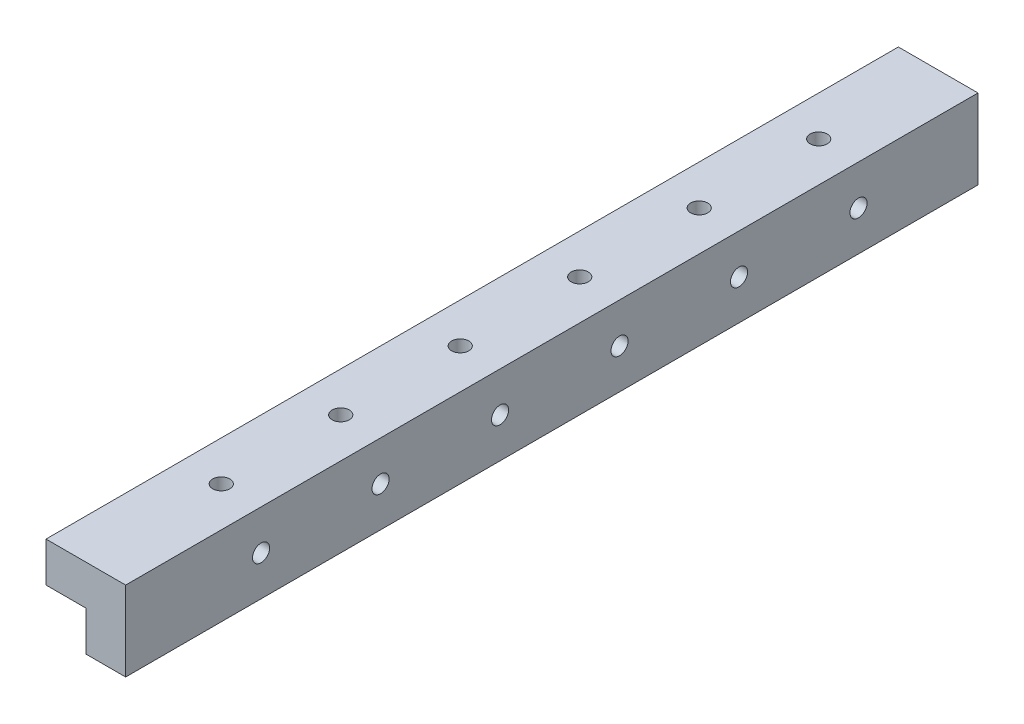
SolidWorks part; units mm, degrees
ref_plane "Front Plane" through (0, 0, 0) normal (0, 0, 1) x (1, 0, 0)
ref_plane "Top Plane" through (0, 0, 0) normal (0, 1, 0) x (1, 0, 0)
ref_plane "Right Plane" through (0, 0, 0) normal (1, 0, 0) x (0, 0, -1)
sketch "Sketch1" plane through (0, 0, 0) normal (0, 0, 1) x (1, 0, 0)
  line L0 (0, -10) -> (10, -10)
  line L1 (10, -10) -> (10, 10)
  line L2 (10, 10) -> (-10, 10)
  line L3 (-10, 10) -> (-10, 0)
  line L4 (-10, 0) -> (0, 0)
  line L5 (0, 0) -> (0, -10)
  point P3 (0, 0)
  dimension "D1" = 10
  dimension "D2" = 20
  dimension "D3" = 10
  dimension "D4" = 20
extrude "Boss-Extrude1" add sketch "Sketch1" against normal blind 214
hole_wizard "Tap Drill for M3x0.5 Tap1" positions "Sketch70" profile "Sketch72" hole size "M3x0.5" standard "ANSI Metric"
sketch "Sketch70" plane through (10, 0, 0) normal (1, 0, 0) x (0, 0, -1)
  line L0 (214, -10) -> (214, 10) construction
  point P0 (34, 0)
  point P3 (64, 0)
  point P6 (94, 0)
  point P9 (124, 0)
  point P12 (154, 0)
  point P15 (184, 0)
  dimension "D1" = 34
  dimension "D2" = 30
  dimension "D3" = 60
  dimension "D4" = 90
  dimension "D5" = 120
  dimension "D6" = 150
  dimension "D7" = 30
sketch "Sketch72" plane through (10, 0, -34) normal (0, 1, 0) x (0, 0, -1)
  line L0 (0, 0) -> (0, 6.825)
  line L1 (0, 6.825) -> (2.15, 6.825)
  line L2 (2.15, 6.825) -> (2.15, 0)
  line L5 (2.15, 0) -> (0, 0)
  line L10 (0, 6.825) -> (-2.15, 6.825) construction
  line L11 (0, -6.35) -> (0, 107.95) construction
  dimension "Hole Dia." = 4.3
  dimension "Hole Depth" = 6.825
  dimension "Drill Angle" = 180
hole_wizard "Tap Drill for M3x0.5 Tap2" positions "Sketch75" profile "Sketch76" hole size "M3x0.5" standard "ANSI Metric"
sketch "Sketch75" plane through (0, 10, 0) normal (0, 1, 0) x (1, 0, 0)
  line L0 (10, 0) -> (-10, 0) construction
  line L1 (10, 214) -> (-10, 214) construction
  point P0 (0, 34)
  point P3 (0, 64)
  point P6 (0, 94)
  point P9 (0, 124)
  point P12 (0, 154)
  point P15 (0, 184)
  dimension "D1" = 34
  dimension "D2" = 30
  dimension "D3" = 60
  dimension "D4" = 90
  dimension "D5" = 120
  dimension "D6" = 150
  dimension "D7" = 30
sketch "Sketch76" plane through (0, 10, -34) normal (1, 0, 0) x (0, 0, 1)
  line L0 (0, 0) -> (0, 6.825)
  line L1 (0, 6.825) -> (2.15, 6.825)
  line L2 (2.15, 6.825) -> (2.15, 0)
  line L5 (2.15, 0) -> (0, 0)
  line L10 (0, 6.825) -> (-2.15, 6.825) construction
  line L11 (0, -6.35) -> (0, 107.95) construction
  dimension "Hole Dia." = 4.3
  dimension "Hole Depth" = 6.825
  dimension "Drill Angle" = 180
